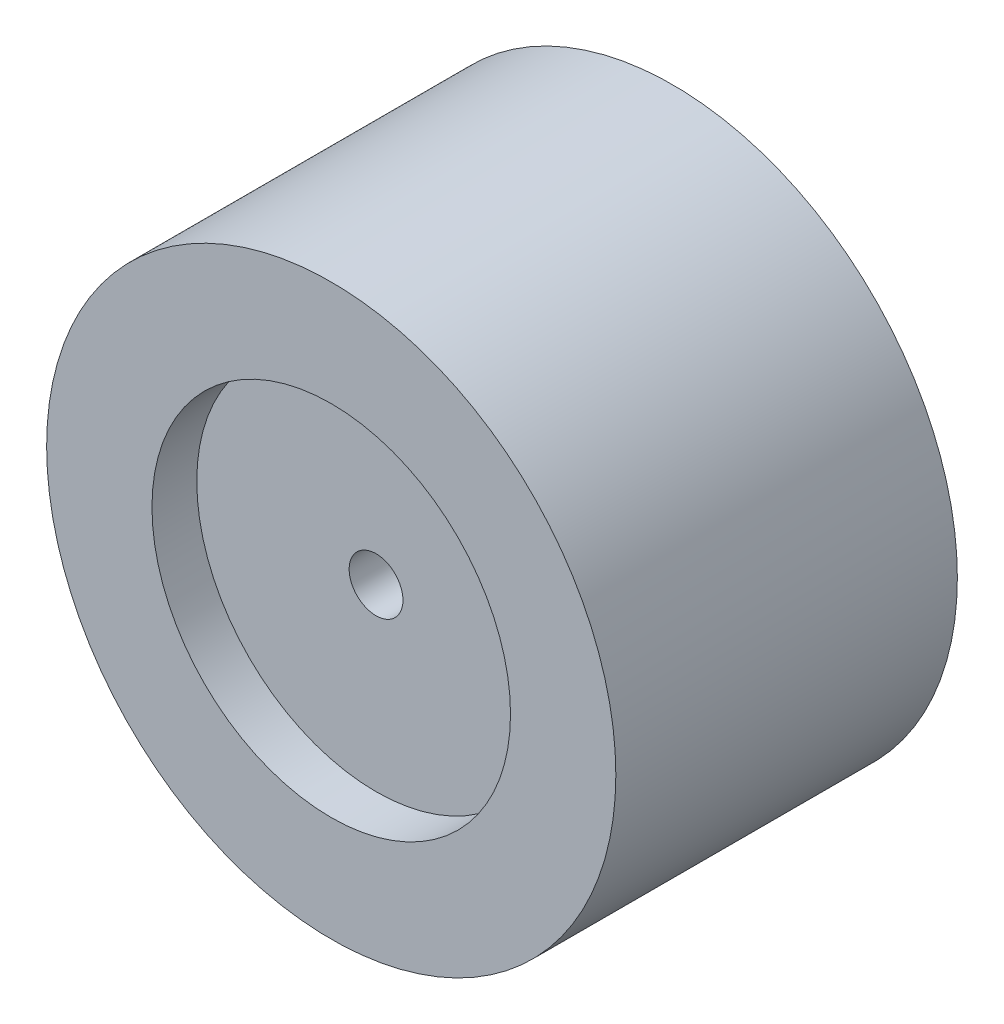
SolidWorks part; units mm, degrees
ref_plane "Plan de face" through (0, 0, 0) normal (0, 0, 1) x (1, 0, 0)
ref_plane "Plan de dessus" through (0, 0, 0) normal (0, 1, 0) x (1, 0, 0)
ref_plane "Plan de droite" through (0, 0, 0) normal (1, 0, 0) x (0, 0, -1)
sketch "Esquisse1" plane through (0, 0, 0) normal (0, 0, 1) x (1, 0, 0)
  circle A0 centre (0, 0) radius 3
  circle A1 centre (0, 0) radius 31.75
  dimension "D1" = 6
  dimension "D2" = 63.5
extrude "Boss.-Extru.1" add sketch "Esquisse1" along normal blind 38.1
sketch "Esquisse2" plane through (0, 0, 38.1) normal (0, 0, 1) x (1, 0, 0)
  circle A0 centre (0, 0) radius 20
  dimension "D1" = 40
extrude "Enlèv. mat.-Extru.1" cut sketch "Esquisse2" against normal blind 5
